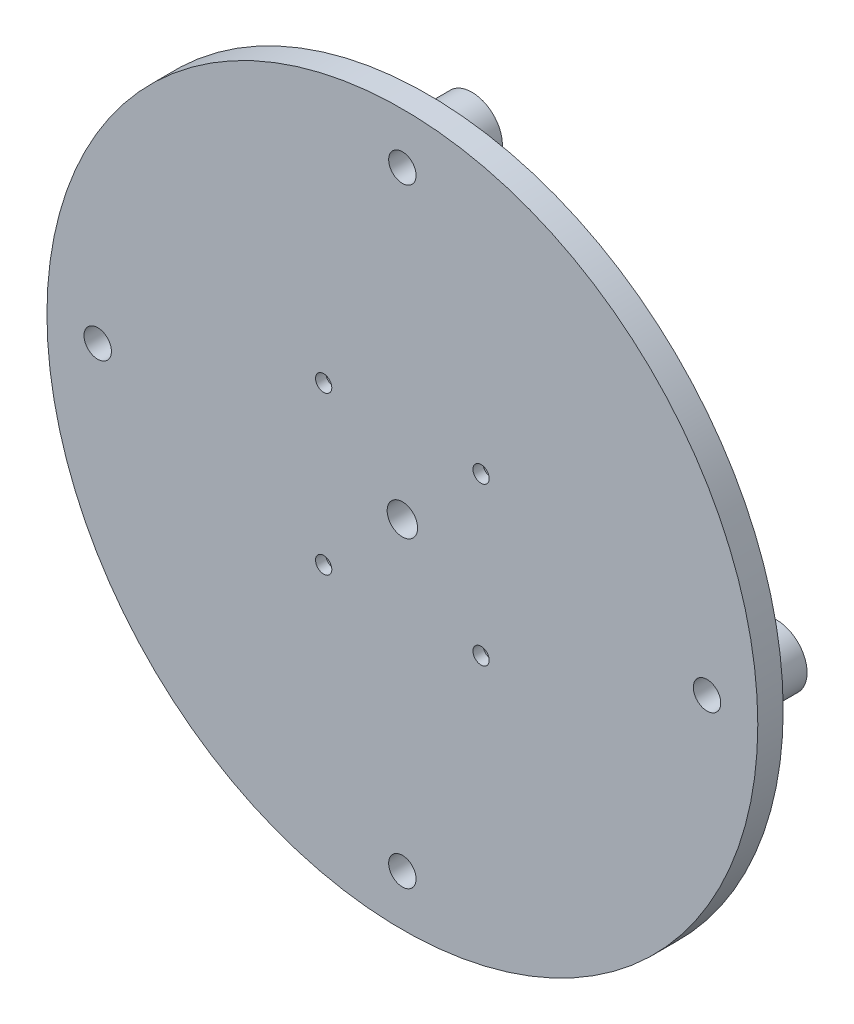
SolidWorks part; units mm, degrees
ref_plane "Front Plane" through (0, 0, 0) normal (0, 0, 1) x (1, 0, 0)
ref_plane "Top Plane" through (0, 0, 0) normal (0, 1, 0) x (1, 0, 0)
ref_plane "Right Plane" through (0, 0, 0) normal (1, 0, 0) x (0, 0, -1)
sketch "Sketch1" plane through (0, 0, 0) normal (0, 0, 1) x (1, 0, 0)
  circle A0 centre (0, 0) radius 70
extrude "Boss-Extrude1" add sketch "Sketch1" along normal blind 5
sketch "Sketch2" plane through (0, 0, 5) normal (0, 0, 1) x (1, 0, 0)
  circle A0 centre (0, 0) radius 60
  circle A1 centre (0, 60) radius 1.6
  circle A2 centre (60, 0) radius 1.6
  circle A3 centre (0, -60) radius 1.6
  circle A4 centre (-60, 0) radius 1.6
  point P13 (0, 0)
  dimension "D1" = 4
extrude "Cut-Extrude1" cut sketch "Sketch2" against normal blind 15 contours A1 | A4 | A3 | A2
sketch "Sketch3" plane through (0, 0, 5) normal (0, 0, 1) x (1, 0, 0)
  circle A0 centre (0, 0) radius 3
extrude "Cut-Extrude2" cut sketch "Sketch3" against normal blind 5
sketch "Sketch4" plane through (0, 0, 5) normal (0, 0, 1) x (1, 0, 0)
  line L1 (-15.5, -15.5) -> (15.5, -15.5)
  line L2 (-15.5, -15.5) -> (-15.5, 15.5)
  line L3 (-15.5, 15.5) -> (15.5, 15.5)
  line L4 (15.5, -15.5) -> (15.5, 15.5)
  line L5 (-15.5, -15.5) -> (15.5, 15.5) construction
  line L6 (-15.5, 15.5) -> (15.5, -15.5) construction
  circle A0 centre (-15.5, 15.5) radius 1.6
  circle A1 centre (15.5, 15.5) radius 1.6
  circle A2 centre (15.5, -15.5) radius 1.6
  circle A3 centre (-15.5, -15.5) radius 1.6
  point P0 (0, 0)
  point P16 (0, 0)
  dimension "D1" = 4
extrude "Cut-Extrude3" cut sketch "Sketch4" against normal blind 5 contours A0 | A1 | A2 | A3
sketch "Sketch5" plane through (0, 0, 0) normal (0, 0, -1) x (-1, 0, 0)
  circle A0 centre (-15.5, 15.5) radius 2.8
  circle A1 centre (15.5, 15.5) radius 2.8
  circle A2 centre (15.5, -15.5) radius 2.8
  circle A3 centre (-15.5, -15.5) radius 2.8
  point P12 (0, 0)
  dimension "D1" = 4
extrude "Cut-Extrude4" cut sketch "Sketch5" against normal blind 3
sketch "Sketch6" plane through (0, 0, 0) normal (0, 0, -1) x (-1, 0, 0)
  circle A0 centre (0, 60) radius 6
  circle A1 centre (60, 0) radius 6
  circle A2 centre (0, -60) radius 6
  circle A3 centre (-60, 0) radius 6
  point P12 (0, 0)
  dimension "D1" = 4
extrude "Boss-Extrude2" add sketch "Sketch6" along normal blind 8.7
sketch "Sketch7" plane through (0, 0, 5) normal (0, 0, 1) x (1, 0, 0)
  circle A0 centre (0, -60) radius 1.6 construction
  circle A1 centre (-60, 0) radius 1.6 construction
  circle A2 centre (0, 60) radius 1.6 construction
  circle A3 centre (60, 0) radius 1.6 construction
  circle A4 centre (0, -60) radius 1.6
  circle A5 centre (-60, 0) radius 1.6
  circle A6 centre (0, 60) radius 1.6
  circle A7 centre (60, 0) radius 1.6
extrude "Cut-Extrude5" cut sketch "Sketch7" against normal blind 15
sketch "Sketch8" plane through (0, 0, 5) normal (0, 0, 1) x (1, 0, 0)
  circle A0 centre (0, 60) radius 2.7
  circle A1 centre (60, 0) radius 2.7
  circle A2 centre (0, -60) radius 2.7
  circle A3 centre (-60, 0) radius 2.7
  point P12 (0, 0)
  dimension "D1" = 4
extrude "Cut-Extrude6" cut sketch "Sketch8" against normal blind 4
